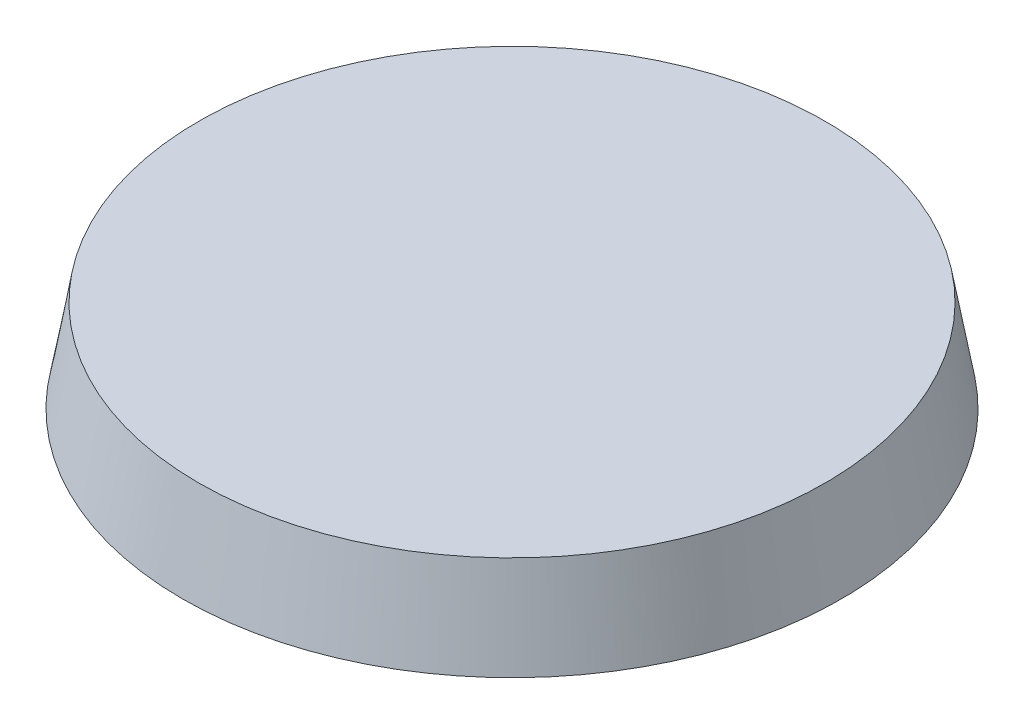
SolidWorks part; units mm, degrees
ref_plane "Спереди" through (0, 0, 0) normal (0, 0, 1) x (1, 0, 0)
ref_plane "Сверху" through (0, 0, 0) normal (0, 1, 0) x (1, 0, 0)
ref_plane "Справа" through (0, 0, 0) normal (1, 0, 0) x (0, 0, -1)
sketch "Эскиз1" plane through (0, 0, 0) normal (0, 1, 0) x (1, 0, 0)
  circle A0 centre (0, 0) radius 12.5
extrude "Бобышка-Вытянуть1" add sketch "Эскиз1" along normal blind 3.5 draft 10
